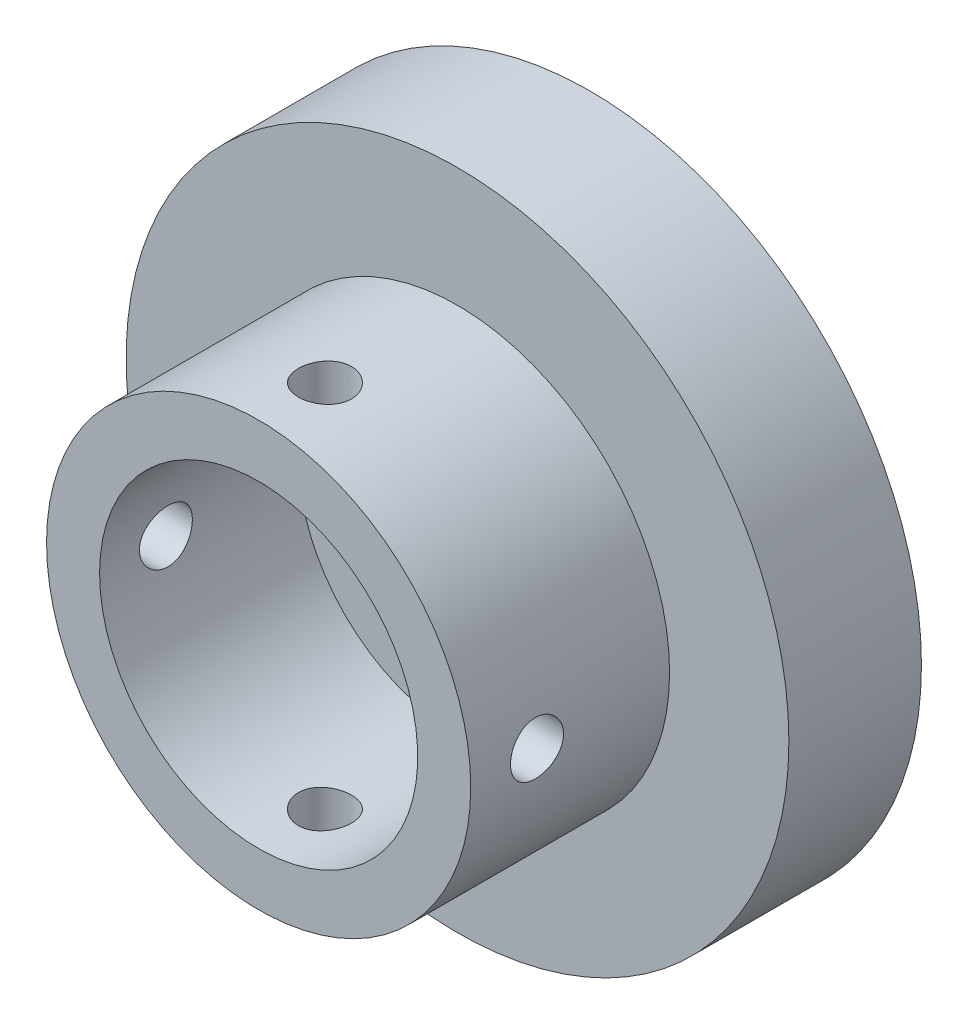
SolidWorks part; units mm, degrees
ref_plane "Ebene vorne" through (0, 0, 0) normal (0, 0, 1) x (1, 0, 0)
ref_plane "Ebene oben" through (0, 0, 0) normal (0, 1, 0) x (1, 0, 0)
ref_plane "Ebene rechts" through (0, 0, 0) normal (1, 0, 0) x (0, 0, -1)
sketch "Skizze1" plane through (0, 0, 0) normal (0, 0, 1) x (1, 0, 0)
  circle A1 centre (0, 0) radius 12.5
  dimension "D2" = 25
extrude "Aufsatz-Linear austragen1" add sketch "Skizze1" along normal blind 40
sketch "Skizze2" plane through (0, 0, 0) normal (1, 0, 0) x (0, 0, -1)
  line L0 (-35, -12.5) -> (-35, -8)
  line L1 (-40, -12.5) -> (0, -12.5) construction
  line L2 (-35, -8) -> (-5, -8)
  line L3 (-5, -8) -> (-5, -12.5)
  line L4 (-35, -12.5) -> (-33.9743, -17.5)
  line L5 (-33.9743, -17.5) -> (-5, -12.5)
  line L6 (0, -12.5) -> (0, 12.5) construction
  line L7 (-35, -12.5) -> (-5, -12.5) construction
  line L8 (-8.1553, -12.5) -> (0, -12.5) construction
  line L9 (0, -12.5) -> (0, -2.7012) construction
  point P0 (-40, -12.5)
  point P1 (-40, 12.5)
  point P11 (0, -12.5)
  point P16 (-20, -12.5)
  dimension "D1" = 5
  dimension "D2" = 5
  dimension "D3" = 90
  dimension "D4" = 4.5
  dimension "D5" = 5
sketch "Skizze3" plane through (0, 0, 0) normal (1, 0, 0) x (0, 0, -1)
  line L0 (-40, 12.5) -> (-40, -12.5) construction
  line L1 (-40, 0) -> (0, 0) construction
  point P0 (-40, -12.5)
  point P1 (-40, 12.5)
  point P3 (0, 12.5)
  point P5 (0, -12.5)
  point P7 (-40, 0)
  point P9 (0, 0)
  point P15 (0, 0)
  point P16 (-40, -12.5)
revolve "Schnitt-Rotation3" cut sketch "Skizze2" angle 360 about L1
sketch "Skizze4" plane through (0, 0, 0) normal (0, 0, 1) x (1, 0, 0)
  circle A0 centre (0, 0) radius 12
  circle A1 centre (0, 0) radius 15
  dimension "D1" = 24
  dimension "D2" = 30
extrude "Schnitt-Linear austragen1" cut sketch "Skizze4" along normal blind 20 from offset 30
sketch "Skizze5" plane through (0, 0, 40) normal (0, 0, 1) x (1, 0, 0)
  line L0 (0, -14.9663) -> (0, 15.9993) construction
  line L1 (0, 0) -> (-5.4573, 6.5037) construction
  circle A0 centre (0, 0) radius 12 construction
  circle A2 centre (-5.4573, 6.5037) radius 1.1
  circle A3 centre (6.5037, 5.4573) radius 1.1
  circle A4 centre (5.4573, -6.5037) radius 1.1
  circle A5 centre (-6.5037, -5.4573) radius 1.1
  point P0 (0, 0)
  point P4 (0, 12.5)
  point P5 (0, -12.5)
  point P7 (0, 12)
  point P9 (0, -12)
  point P35 (0, 0)
  dimension "D3" = 2.2
  dimension "D2" = 40
  dimension "D4" = 4
extrude "Schnitt-Linear austragen2" cut sketch "Skizze5" against normal blind 20
sketch "Skizze6" plane through (0, 0, 0) normal (0, 0, -1) x (-1, 0, 0)
  line L0 (-16.5904, 0) -> (16.1056, 0) construction
  line L1 (0, 15.8638) -> (0, -16.2225) construction
  circle A0 centre (-2.25, 0) radius 1
  circle A1 centre (0, 2.25) radius 1
  circle A2 centre (2.25, 0) radius 1
  circle A3 centre (0, -2.25) radius 1
  point P0 (0, 0)
  point P6 (0, 0)
  point P7 (-1.25, 0)
  point P9 (-2.25, 0)
  point P14 (0, 0)
  point P17 (0, 0)
  point P20 (0, 0)
  point P23 (0, 0)
  dimension "D1" = 1.25
  dimension "D2" = 4
  dimension "D3" = 1
extrude "Schnitt-Linear austragen3" cut sketch "Skizze6" against normal blind 10
sketch "Skizze7" plane through (0, 0, 0) normal (1, 0, 0) x (0, 0, -1)
  line L0 (-40, 0) -> (0, 0) construction
  line L1 (-5.0699, 0) -> (-35.075, 0)
  line L2 (-40, 0) -> (-42.3132, 0)
  line L3 (-35, -6) -> (-5, -6)
  line L4 (-35, -12) -> (-35, 12) construction
  line L5 (-5, 8) -> (-5, -8) construction
  line L6 (-5, -6) -> (-5.0699, 0)
  line L8 (-35, -8) -> (-5, -8) construction
  line L9 (-35, -6) -> (-40, -6)
  line L10 (-40, 12) -> (-40, -12) construction
  line L11 (-35.075, 0) -> (-40, 0)
  line L12 (-42.3132, 0) -> (-42.3132, -6)
  line L13 (-42.3132, -6) -> (-40, -6)
  point P0 (-5.0699, 0)
  point P1 (-35.075, 0)
  dimension "D1" = 2
revolve "Schnitt-Rotation4" cut sketch "Skizze7" angle 360 about L1
sketch "Skizze8" plane through (0, 0, 0) normal (0, 0, 1) x (1, 0, 0)
  line L1 (12.5, 12.5) -> (-12.5, 12.5)
  line L2 (12.5, 12.5) -> (12.5, -12.5)
  line L3 (12.5, -12.5) -> (-12.5, -12.5)
  line L4 (-12.5, 12.5) -> (-12.5, -12.5)
  line L5 (12.5, 12.5) -> (-12.5, -12.5) construction
  line L6 (12.5, -12.5) -> (-12.5, 12.5) construction
  circle A0 centre (0, 0) radius 12.5 construction
  point P0 (0, 0)
  point P1 (0, 0)
  point P8 (0, -12.5)
  point P9 (0, -12.5)
  point P10 (12.5, 0)
  point P12 (0, 0)
  point P13 (12.5, 0)
extrude "Schnitt-Linear austragen4" cut sketch "Skizze8" along normal through all from offset 12.5
sketch "Skizze9" plane through (0, 0, 0) normal (1, 0, 0) x (0, 0, -1)
  line L0 (-40, 0) -> (0, 0) construction
  circle A0 centre (-10, 0) radius 1
  dimension "D1" = 2
  dimension "D2" = 10
extrude "Schnitt-Linear austragen5" cut sketch "Skizze9" against normal through all both and the other way through all
sketch "Skizze10" plane through (0, 0, 0) normal (0, 1, 0) x (1, 0, 0)
  line L0 (0, -40) -> (0, 0) construction
  circle A0 centre (0, -10) radius 1
  dimension "D1" = 2
  dimension "D2" = 10
extrude "Schnitt-Linear austragen6" cut sketch "Skizze10" against normal through all both and the other way through all
